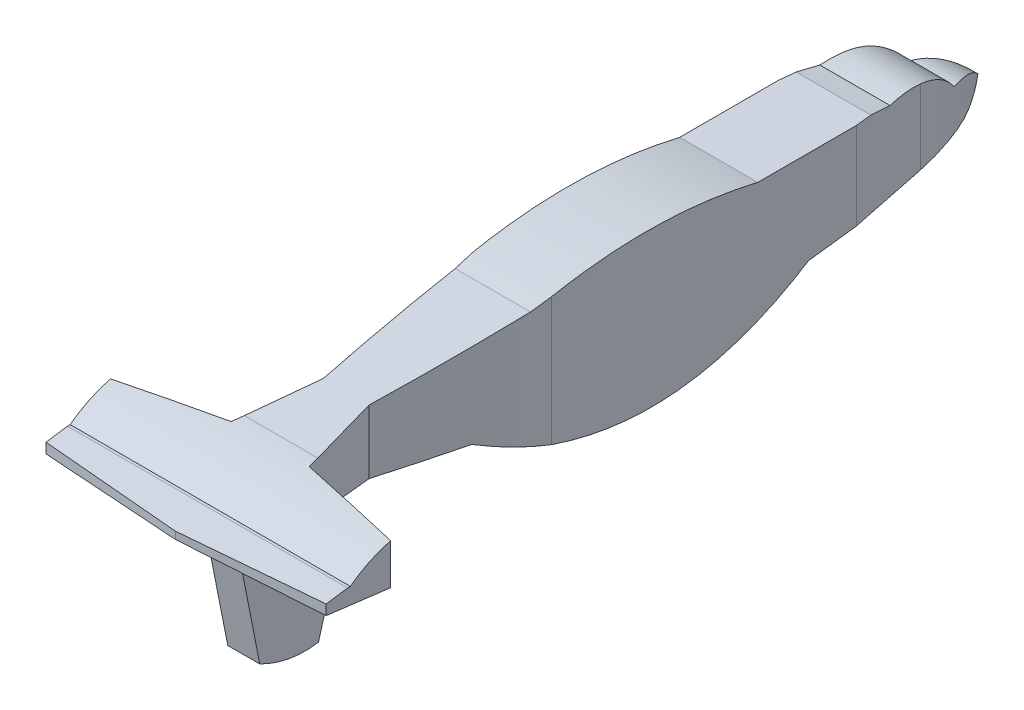
SolidWorks part; units mm, degrees
material "Balsa"
ref_plane "Front Plane" through (0, 0, 0) normal (0, 0, 1) x (1, 0, 0)
ref_plane "Top Plane" through (0, 0, 0) normal (0, 1, 0) x (1, 0, 0)
ref_plane "Right Plane" through (0, 0, 0) normal (1, 0, 0) x (0, 0, -1)
sketch "Sketch3" plane through (0, 0, 0) normal (0, 1, 0) x (1, 0, 0)
  line L0 (158.9857, 11.7628) -> (158.9857, 511.7628) construction
  line L1 (137.9704, 414.2729) -> (137.9704, 223.6934)
  line L2 (148.0447, 119.6103) -> (137.9704, 72.0713)
  line L3 (137.9704, 72.0713) -> (74.7774, 59.755)
  line L4 (74.7774, 59.755) -> (74.7774, 19.4469)
  line L5 (74.7774, 19.4469) -> (162.3914, 12.7289)
  line L6 (162.3914, 514.7376) -> (162.3914, -15.47) construction
  line L7 (137.9704, 414.2729) -> (142.643, 458.9435)
  line L8 (186.8125, 414.2729) -> (182.1399, 458.9435)
  line L9 (250.0055, 19.4469) -> (162.3914, 12.7289)
  line L10 (250.0055, 59.755) -> (250.0055, 19.4469)
  line L11 (186.8125, 72.0713) -> (250.0055, 59.755)
  line L12 (176.7381, 119.6103) -> (186.8125, 72.0713)
  line L13 (186.8125, 414.2729) -> (186.8125, 223.6934)
  spline S0 degree 2 poles (137.9704, 223.6934) (141.477, 171.478) (148.0447, 119.6103) knots 0 0 0 0.887153 0.887153 0.887153
  spline S1 degree 2 poles (142.643, 458.9435) (146.3896, 491.0218) (162.3914, 514.7376) knots 0 0 0 0.490133 0.490133 0.490133
  spline S2 degree 2 poles (182.1399, 458.9435) (178.3933, 491.0218) (162.3914, 514.7376) knots 0 0 0 0.490133 0.490133 0.490133
  spline S3 degree 2 poles (186.8125, 223.6934) (183.3059, 171.478) (176.7381, 119.6103) knots 0 0 0 0.887153 0.887153 0.887153
  dimension "D1" = 500
extrude "Boss-Extrude1" add sketch "Sketch3" along normal blind 240
sketch "Sketch4" plane through (0, 0, 0) normal (1, 0, 0) x (0, 0, -1)
  line L0 (13.9063, 87.788) -> (513.9063, 87.788) construction
  line L1 (12.7289, 85.925) -> (46.992, 81.651)
  line L2 (12.7289, 240) -> (12.7289, 0) construction
  line L3 (46.992, 81.651) -> (177.382, 65.3863)
  line L4 (437.733, 119.4468) -> (424.3804, 121.6022)
  line L5 (384.3868, 63.3338) -> (489.694, 76.6634)
  line L6 (514.7376, 240) -> (514.7376, 0) construction
  line L7 (424.3804, 121.6022) -> (352.5927, 121.6022)
  line L8 (211.2973, 121.6022) -> (132.669, 113.795)
  line L9 (132.669, 113.795) -> (78.8492, 108.4511)
  line L10 (32.8586, 93.3774) -> (12.7289, 90.4303)
  line L11 (12.7289, 90.4303) -> (12.7289, 85.925)
  line L12 (32.8586, 93.3774) -> (34.5778, 93.3774)
  spline S0 degree 2 poles (177.382, 65.3863) (287.6403, 1.8623) (384.3868, 63.3338) knots 0 0 0 1 1 1
  spline S1 degree 2 poles (489.694, 76.6634) (505.3177, 77.8093) (514.7376, 87.1364) knots 0 0 0 0.756427 0.756427 0.756427
  spline S2 degree 2 poles (514.7376, 87.1364) (501.3821, 101.2954) (485.8856, 101.6082) knots 0 0 0 0.708119 0.708119 0.708119
  spline S3 degree 3 poles (485.8856, 101.6082) (473.9435, 117.0772) (457.8926, 123.0234) (437.733, 119.4468) knots 0 0 0 0 0.856301 0.856301 0.856301 0.856301
  spline S4 degree 2 poles (352.5927, 121.6022) (283.1607, 138.1352) (211.2973, 121.6022) knots 0 0 0 1 1 1
  spline S5 degree 2 poles (78.8492, 108.4511) (52.3096, 107.1078) (34.5778, 93.3774) knots 0 0 0 0.568418 0.568418 0.568418
  dimension "D1" = 500
extrude "Cut-Extrude1" cut sketch "Sketch4" along normal through all flip side to cut
ref_plane "Plane1" through (162.3914, 0, 0) normal (-1, 0, 0) x (0, 0, 1)
sketch "Sketch5" plane through (162.3914, 0, 0) normal (-1, 0, 0) x (0, 0, 1)
  line L0 (-376.9315, 54.0204) -> (-138.2648, 54.0204) construction
  line L1 (-508.8176, 86.8496) -> (-8.8176, 86.8496) construction
  line L2 (-39.6009, 82.573) -> (-55.5277, 2.0657)
  line L3 (-19.4469, 85.087) -> (-59.755, 80.059) construction
  line L4 (-92.2639, -4.4763) -> (-107.8642, 50.8796)
  line L5 (-107.8642, 50.8796) -> (-107.8642, 74.0579)
  line L6 (-72.0713, 78.5226) -> (-119.6103, 72.5927) construction
  line L7 (-107.8642, 74.0579) -> (-39.6009, 82.573)
  spline S0 degree 2 poles (-55.5277, 2.0657) (-74.4405, -7.3938) (-92.2639, -4.4763) knots 0 0 0 0.637969 0.637969 0.637969
  dimension "D1" = 500
extrude "Boss-Extrude2" add sketch "Sketch5" along normal blind 10 and the other way blind 10
